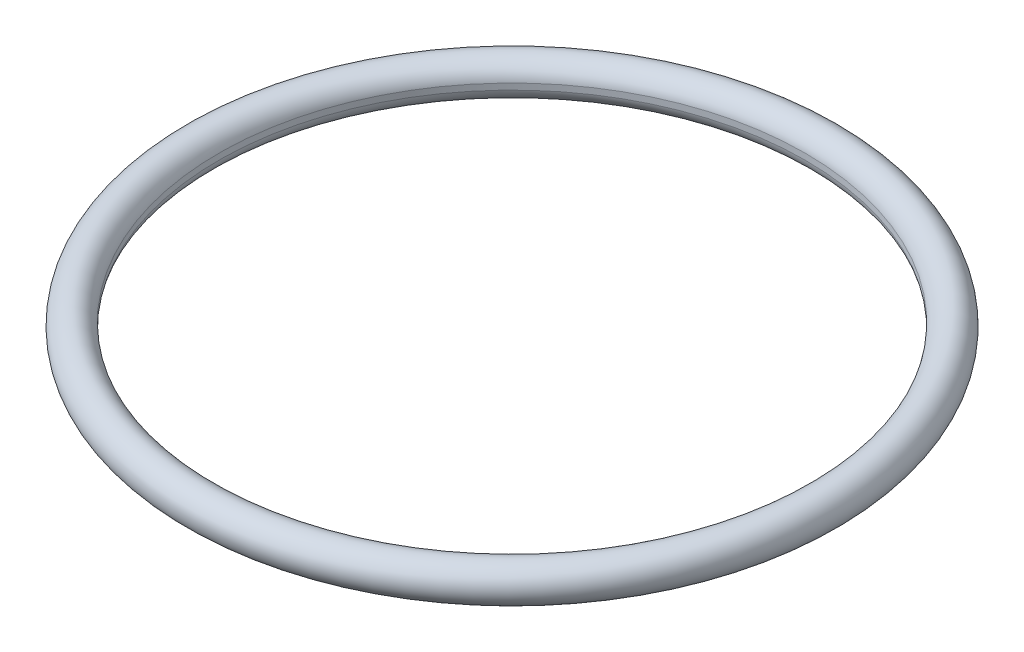
SolidWorks part; units mm, degrees
material "Silicon Rubber"
ref_plane "Front Plane" through (0, 0, 0) normal (0, 0, 1) x (1, 0, 0)
ref_plane "Top Plane" through (0, 0, 0) normal (0, 1, 0) x (1, 0, 0)
ref_plane "Right Plane" through (0, 0, 0) normal (1, 0, 0) x (0, 0, -1)
sketch "Sketch1" plane through (0, 0, 0) normal (0, 0, 1) x (1, 0, 0)
  line L0 (0, 0) -> (0, 23.9875) construction
  line L1 (-24.021, -0.25) -> (-24.021, 0.25)
  arc A0 (-24.021, 0.25) -> (-24.021, -0.25) centre (-25.5, 0) ccw
  point P7 (-24.021, 0)
  dimension "D1" = 25.5
  dimension "D2" = 3
  dimension "D3" = 0.5
revolve "Revolve1" add sketch "Sketch1" angle 360 about L0
